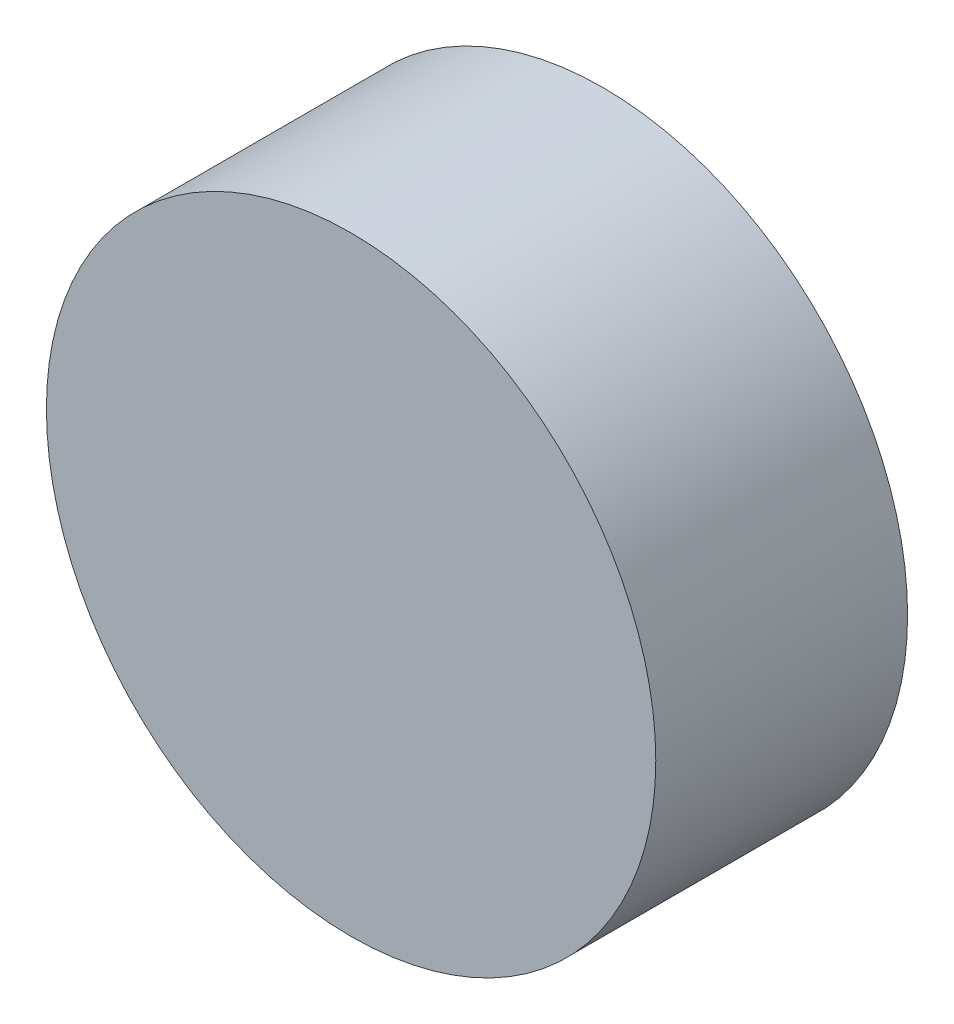
SolidWorks part; units mm, degrees
ref_plane "Front Plane" through (0, 0, 0) normal (0, 0, 1) x (1, 0, 0)
ref_plane "Top Plane" through (0, 0, 0) normal (0, 1, 0) x (1, 0, 0)
ref_plane "Right Plane" through (0, 0, 0) normal (1, 0, 0) x (0, 0, -1)
sketch "Sketch1" plane through (0, 0, 0) normal (0, 0, 1) x (1, 0, 0)
  circle A0 centre (0, 0) radius 3.025
  dimension "D1" = 6.05
extrude "Boss-Extrude1" add sketch "Sketch1" along normal blind 2.5
